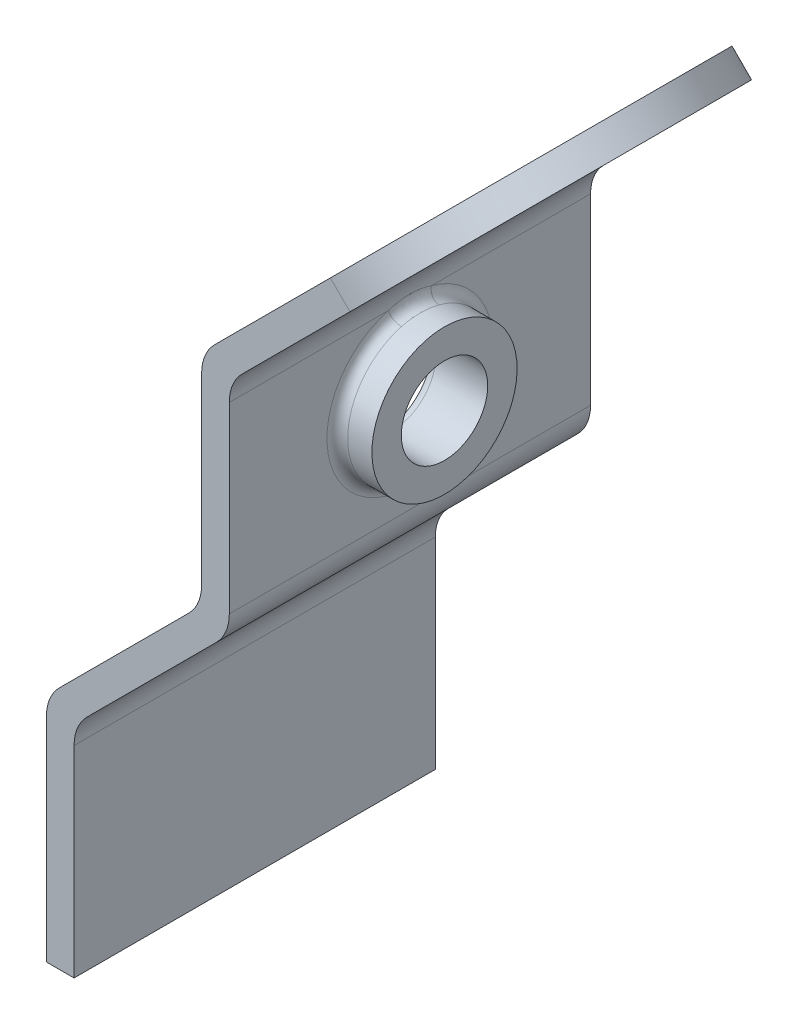
SolidWorks part; units mm, degrees
material "Ductile Iron"
ref_plane "Front Plane" through (0, 0, 0) normal (0, 0, 1) x (1, 0, 0)
ref_plane "Top Plane" through (0, 0, 0) normal (0, 1, 0) x (1, 0, 0)
ref_plane "Right Plane" through (0, 0, 0) normal (1, 0, 0) x (0, 0, -1)
sketch "Sketch1" plane through (0, 0, 0) normal (0, 0, 1) x (1, 0, 0)
  line L0 (1.6, 0) -> (1.6, 11.6479)
  line L1 (2.3439, 13.4439) -> (9.8363, 20.9363)
  line L2 (10.5803, 22.7324) -> (10.5803, 33.3282)
  line L3 (11.3242, 35.1242) -> (24.9487, 48.7487)
  line L4 (24.9487, 48.7487) -> (23.8173, 49.88)
  line L5 (23.8173, 49.88) -> (9.7242, 35.7869)
  line L6 (8.9803, 33.9909) -> (8.9803, 23.3951)
  line L7 (8.2363, 21.599) -> (0.7439, 14.1067)
  line L8 (0, 12.3106) -> (0, 0)
  line L9 (0, 0) -> (1.6, 0)
  arc A0 (9.7242, 35.7869) -> (8.9803, 33.9909) centre (11.5203, 33.9909) ccw
  arc A1 (10.5803, 33.3282) -> (11.3242, 35.1242) centre (13.1203, 33.3282) cw
  arc A2 (8.9803, 23.3951) -> (8.2363, 21.599) centre (6.4403, 23.3951) cw
  arc A3 (9.8363, 20.9363) -> (10.5803, 22.7324) centre (8.0403, 22.7324) ccw
  arc A4 (1.6, 11.6479) -> (2.3439, 13.4439) centre (4.14, 11.6479) cw
  arc A5 (0.7439, 14.1067) -> (0, 12.3106) centre (2.54, 12.3106) ccw
  point P19 (10.5803, 34.3803)
  point P24 (10.5803, 21.6803)
  point P27 (1.6, 12.7)
  dimension "D12" = 2.54
  dimension "D1" = 1.6
  dimension "D2" = 135
  dimension "D3" = 135
  dimension "D4" = 135
  dimension "D5" = 1.6
  dimension "D6" = 1.6
  dimension "D7" = 1.6
  dimension "D8" = 12.7
  dimension "D9" = 12.7
  dimension "D10" = 12.7
  dimension "D11" = 20.32
extrude "Boss-Extrude1" add sketch "Sketch1" against normal blind 20.9
sketch "Sketch3" plane through (-13.0314, 13.0314, 0) normal (-0.7071, 0.7071, 0) x (0, 0, 1)
  line L4 (0, 32.1812) -> (0, 52.1119)
  line L5 (0, 52.1119) -> (-20.9, 52.1119)
  line L6 (-20.9, 52.1119) -> (-20.9, 32.1812)
  line L7 (-20.9, 32.1812) -> (0, 32.1812)
  line L8 (0, 41.6619) -> (0, 52.1119)
  line L9 (0, 52.1119) -> (-20.9, 52.1119)
  line L10 (-20.9, 52.1119) -> (-20.9, 41.6619)
  arc A1 (0, 41.6619) -> (-20.9, 41.6619) centre (-10.45, 41.6619) ccw
  line M6 (0, 32.1812) -> (0, 52.1119)
  line M7 (0, 52.1119) -> (-20.9, 52.1119)
  line M8 (-20.9, 52.1119) -> (-20.9, 32.1812)
  dimension "D1" = 0
extrude "Cut-Extrude1" cut sketch "Sketch3" against normal through all contours A1 L9 M8 | A1 M6 M7
sketch "Sketch4" plane through (8.9803, 0, 0) normal (-1, 0, 0) x (0, 0, 1)
  line L1 (0, 33.9909) -> (0, 23.3951) construction
  line L4 (-20.9, 33.9909) -> (0, 33.9909) construction
  circle A0 centre (-10.45, 28.693) radius 2.5
  dimension "D1" = 5
  dimension "D2" = 5.2979
  dimension "D3" = 10.45
extrude "Cut-Extrude2" cut sketch "Sketch4" against normal through all
sketch "Sketch5" plane through (10.5803, 0, 0) normal (1, 0, 0) x (0, 0, -1)
  circle A0 centre (10.45, 28.693) radius 4.2
  circle A2 centre (10.45, 28.693) radius 2.5 construction
  circle A3 centre (10.45, 28.693) radius 2.5
  dimension "D1" = 1.7
extrude "Boss-Extrude2" add sketch "Sketch5" along normal blind 2
fillet "Fillet1" radius 0.6 2 edges at (8.9803, 26.193, -10.45) (10.5803, 32.893, -10.45)
